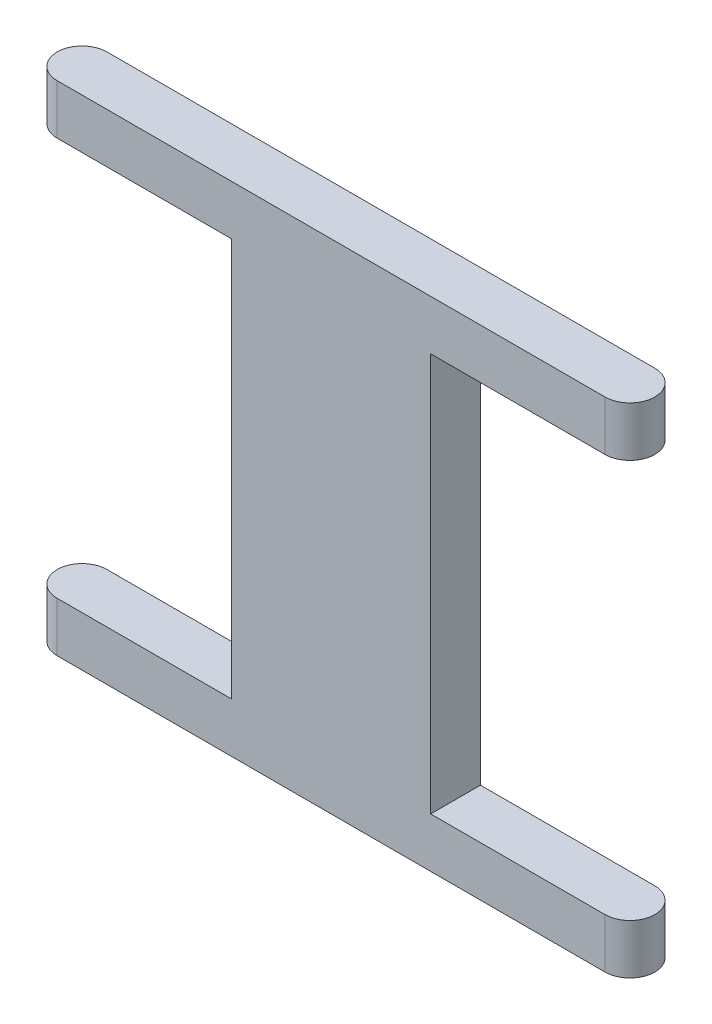
SolidWorks part; units mm, degrees
ref_plane "Front" through (0, 0, 0) normal (0, 0, 1) x (1, 0, 0)
ref_plane "Top" through (0, 0, 0) normal (0, 1, 0) x (1, 0, 0)
ref_plane "Right" through (0, 0, 0) normal (1, 0, 0) x (0, 0, -1)
sketch "草图1" plane through (0, 0, 0) normal (0, 1, 0) x (1, 0, 0)
  line L0 (-11, 0) -> (11, 0) construction
  line L1 (-11, 1) -> (11, 1)
  line L2 (-11, -1) -> (11, -1)
  arc A0 (-11, 1) -> (-11, -1) centre (-11, 0) ccw
  arc A1 (11, -1) -> (11, 1) centre (11, 0) ccw
  point P2 (0, 0)
extrude "凸台-拉伸1" add sketch "草图1" along normal blind 20
sketch "草图2" plane through (0, 0, -1) normal (0, 0, -1) x (-1, 0, 0)
  line L0 (-12, 10) -> (12, 10) construction
  line L1 (-12, 20) -> (-12, 0) construction
  line L2 (12, 0) -> (12, 20) construction
  line L4 (-12, 18) -> (-4, 18)
  line L5 (-12, 18) -> (-12, 2)
  line L6 (-12, 2) -> (-4, 2)
  line L7 (-4, 18) -> (-4, 2)
  line L8 (12, 18) -> (4, 18)
  line L9 (12, 18) -> (12, 2)
  line L10 (12, 2) -> (4, 2)
  line L11 (4, 18) -> (4, 2)
  dimension "D1" = 16
  dimension "D2" = 8
  dimension "D3" = 8
  dimension "D4" = 16
  dimension "D5" = 8
  dimension "D6" = 8
extrude "切除-拉伸1" cut sketch "草图2" against normal blind 12
